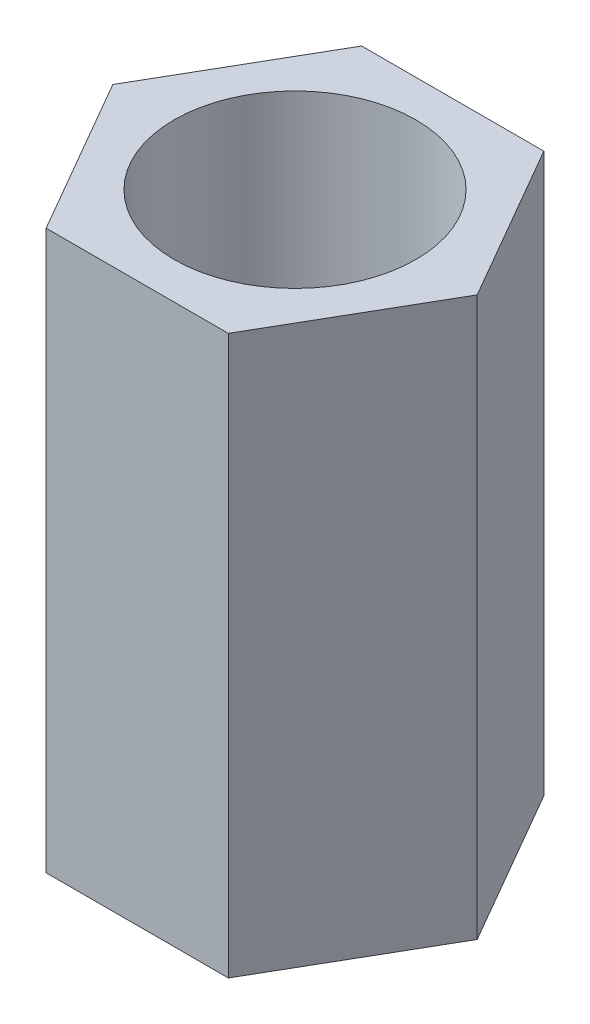
SolidWorks part; units mm, degrees
ref_plane "Front Plane" through (0, 0, 0) normal (0, 0, 1) x (1, 0, 0)
ref_plane "Top Plane" through (0, 0, 0) normal (0, 1, 0) x (1, 0, 0)
ref_plane "Right Plane" through (0, 0, 0) normal (1, 0, 0) x (0, 0, -1)
sketch "Sketch1" plane through (0, 0, 0) normal (0, 1, 0) x (1, 0, 0)
  line L1 (0.979, -1.6957) -> (1.958, 0)
  line L2 (1.958, 0) -> (0.979, 1.6957)
  line L3 (0.979, 1.6957) -> (-0.979, 1.6957)
  line L4 (-0.979, 1.6957) -> (-1.958, 0)
  line L5 (-1.958, 0) -> (-0.979, -1.6957)
  line L6 (-0.979, -1.6957) -> (0.979, -1.6957)
  circle A0 centre (0, 0) radius 1.6957 construction
  circle A1 centre (0, 0) radius 1.3
  dimension "D1" = 2.6
extrude "Boss-Extrude1" add sketch "Sketch1" along normal blind 6
